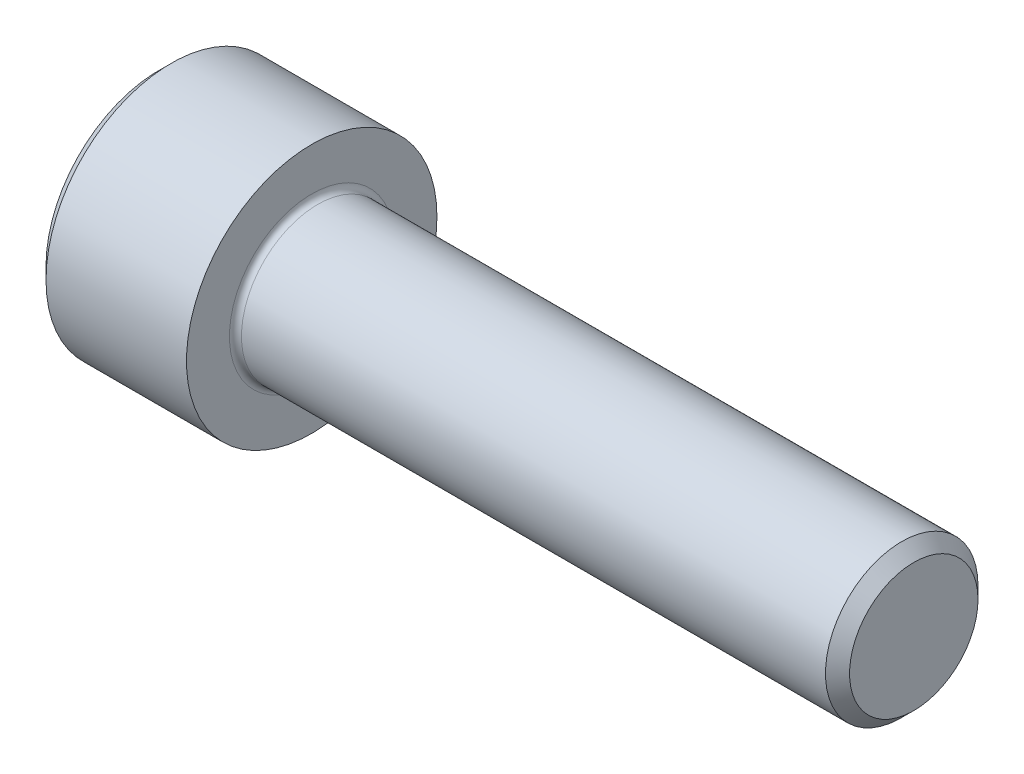
SolidWorks part; units mm, degrees
material "Alloy Steel"
ref_plane "Z Plane" through (0, 0, 0) normal (0, 0, 1) x (1, 0, 0)
ref_plane "Y Plane" through (0, 0, 0) normal (0, 1, 0) x (1, 0, 0)
ref_plane "X Plane" through (0, 0, 0) normal (1, 0, 0) x (0, 0, -1)
sketch "Sketch1" plane through (0, 0, 0) normal (0, 1, 0) x (1, 0, 0)
  line L0 (0, 3.9624) -> (0, -3.9624) construction
  line L1 (0, 0) -> (0, 3.9624)
  line L2 (0, 3.9624) -> (4.826, 3.9624)
  line L3 (4.826, 3.9624) -> (4.826, 2.413)
  line L4 (4.826, 2.413) -> (23.876, 2.413)
  line L5 (23.876, 2.413) -> (23.876, -2.413) construction
  line L6 (23.876, 2.413) -> (23.876, 0)
  line L7 (23.876, 0) -> (0, 0)
  line L8 (0, -3.9624) -> (1.6087, -3.9624) construction
  line L9 (1.6087, -3.9624) -> (3.2173, -3.9624) construction
  line L10 (3.2173, -3.9624) -> (4.826, -3.9624) construction
  point P2 (0, 0)
  point P5 (23.876, 0)
  dimension "Head Diameter" = 7.9248
  dimension "Thread Diameter" = 4.826
  dimension "Thread Length" = 19.05
revolve "Body" add sketch "Sketch1" angle 360 about L7
ref_plane "Plane1" through (3.2173, 0, 0) normal (1, 0, 0) x (0, 0, -1)
sketch "Sketch2" plane through (0, 0, 0) normal (-1, 0, 0) x (0, 0, 1)
  line L1 (-2.2914, 0) -> (-1.1457, -1.9844)
  line L2 (-1.1457, -1.9844) -> (1.1457, -1.9844)
  line L3 (1.1457, -1.9844) -> (2.2914, 0)
  line L4 (2.2914, 0) -> (1.1457, 1.9844)
  line L5 (1.1457, 1.9844) -> (-1.1457, 1.9844)
  line L6 (-1.1457, 1.9844) -> (-2.2914, 0)
  circle A0 centre (0, 0) radius 1.9844 construction
  dimension "Hex Head" = 3.9688
extrude "Hex" cut sketch "Sketch2" against normal up to surface (3.2173 mm away)
chamfer "Chamfer1" distance 0.381 angle 45 2 edges at (23.876, 0, -2.413) (0, 0, -3.9624)
fillet "Fillet1" radius 0.1905 1 edges at (4.826, 0, -2.413)
sketch "Sketch3" plane through (0, 0, 0) normal (1, 0, 0) x (0, 0, -1)
  circle A0 centre (0, 0) radius 2.2914
extrude "Hex Chamfer" cut sketch "Sketch3" along normal blind 2.54 draft 45
